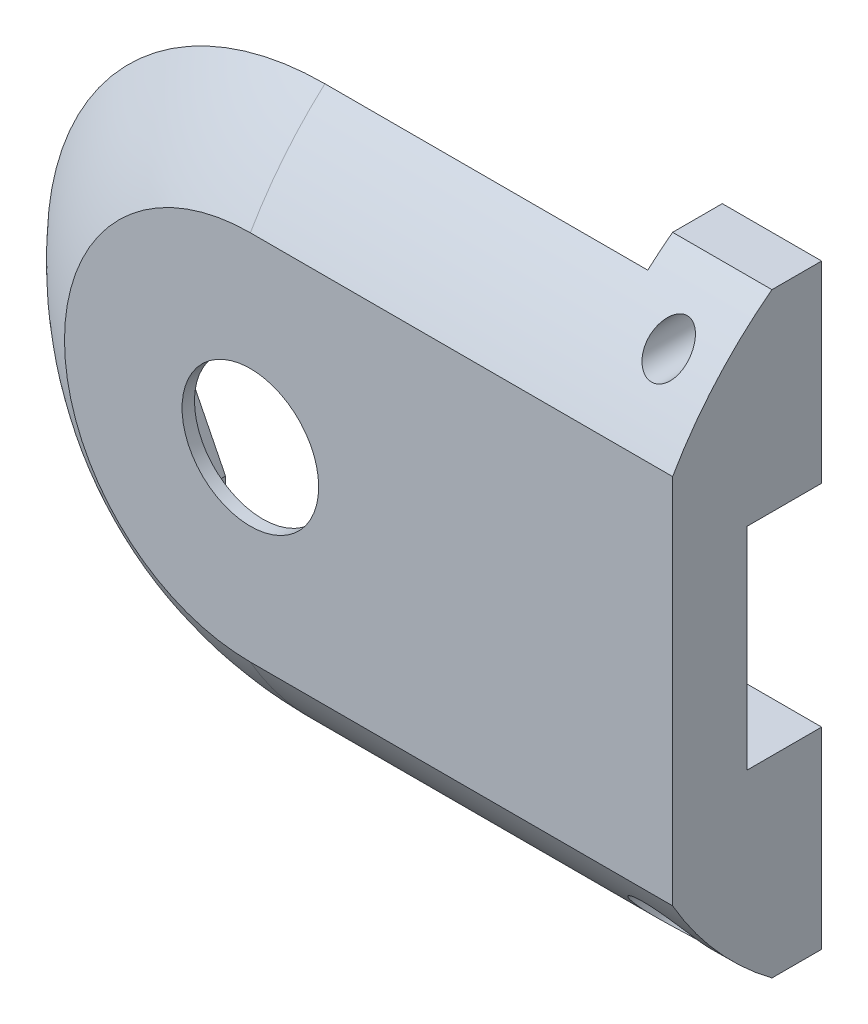
SolidWorks part; units mm, degrees
ref_plane "Front" through (0, 0, 0) normal (0, 0, 1) x (1, 0, 0)
ref_plane "Top" through (0, 0, 0) normal (0, 1, 0) x (1, 0, 0)
ref_plane "Right" through (0, 0, 0) normal (1, 0, 0) x (0, 0, -1)
sketch "Sketch1" plane through (0, 0, 0) normal (0, 0, 1) x (1, 0, 0)
  line L0 (13, 0) -> (17, 0) construction
  line L1 (17, 0) -> (17, 12)
  line L2 (17, 0) -> (17, -12)
  line L3 (0, 0) -> (38, 0) construction
  line L4 (17, 12) -> (5, 12)
  line L6 (17, -12) -> (5, -12)
  circle A0 centre (0, 0) radius 13
  circle A2 centre (0, 0) radius 2.75
extrude "Boss-Extrude1" add sketch "Sketch1" against normal blind 6
sketch "Sketch2" plane through (0, 0, 0) normal (0, 0, 1) x (1, 0, 0)
  line L0 (0, 13) -> (13, 13)
  line L1 (13, 0) -> (13, 4.25) construction
  line L2 (13, 0) -> (13, -4.25) construction
  line L3 (13, 13) -> (13, 0)
  line L4 (13, -4.25) -> (17, -4.25)
  line L5 (13, 0) -> (13, -13)
  line L6 (17, 12) -> (17, -12) construction
  line L7 (13, -13) -> (0, -13)
  line L8 (17, -4.25) -> (17, 4.25)
  line L9 (17, 4.25) -> (13, 4.25)
  circle A0 centre (0, 0) radius 13
extrude "Body Hole" cut sketch "Sketch2" against normal blind 3 from offset 3 offset against normal yes
sketch "Sketch8" plane through (28.2876, 0, 0) normal (0, 0, 1) x (1, 0, 0)
  line L26 (-28.2876, 0) -> (-35.2876, 0) construction
  line L27 (-28.2876, 0) -> (-18.7876, 0) construction
  line L28 (-28.2876, 0) -> (-28.2876, 5.5) construction
  line L29 (-28.2876, 0) -> (-28.2876, -5.5) construction
  line L30 (-35.2876, 0) -> (-35.2876, -1.5)
  line L31 (-35.2876, -1.5) -> (-33.7876, -1.5)
  line L32 (-33.7876, -1.5) -> (-32.2876, -1.5) construction
  line L33 (-32.2876, -1.5) -> (-32.2876, -4.5) construction
  line L34 (-33.7876, -1.5) -> (-32.2876, -4.5)
  line L35 (-32.2876, -4.5) -> (-32.2876, -5.5)
  line L36 (-32.2876, -5.5) -> (-28.2876, -5.5)
  line L37 (-28.2876, -5.5) -> (-24.0376, -5.5)
  line L38 (-24.0376, -5.5) -> (-24.0376, -4.5)
  line L39 (-24.0376, -4.5) -> (-18.7876, -4.5)
  line L40 (-18.7876, -4.5) -> (-18.7876, 0)
  line L41 (-35.2876, 0) -> (-35.2876, 1.5)
  line L42 (-35.2876, 1.5) -> (-33.7876, 1.5)
  line L43 (-33.7876, 1.5) -> (-32.2876, 1.5) construction
  line L44 (-32.2876, 1.5) -> (-32.2876, 4.5) construction
  line L45 (-33.7876, 1.5) -> (-32.2876, 4.5)
  line L46 (-32.2876, 4.5) -> (-32.2876, 5.5)
  line L47 (-32.2876, 5.5) -> (-28.2876, 5.5)
  line L48 (-28.2876, 5.5) -> (-24.0376, 5.5)
  line L49 (-24.0376, 5.5) -> (-24.0376, 4.5)
  line L50 (-24.0376, 4.5) -> (-18.7876, 4.5)
  line L51 (-18.7876, 4.5) -> (-18.7876, 0)
extrude "Pot Insert" cut sketch "Sketch8" along normal blind 2.5 from offset 3 offset against normal yes
sketch "Sketch3" plane through (0, 0, 0) normal (1, 0, 0) x (0, 0, -1)
  line L0 (0, 0) -> (13, 0) construction
  line L1 (0, 0) -> (-2, 0) construction
  line L2 (13, 15) -> (-2, 15)
  line L3 (-2, 15) -> (-2, 0)
  line L4 (-2, 0) -> (-2, -15)
  line L5 (-2, -15) -> (13, -15)
  circle A0 centre (13, 0) radius 15
extrude "Cut-Extrude2" cut sketch "Sketch3" along normal through all
sketch "Sketch6" plane through (0, 0, 0) normal (1, 0, 0) x (0, 0, -1)
  line L0 (0, 0) -> (13, 0) construction
  line L1 (0, 0) -> (-2, 0) construction
  line L2 (13, 15) -> (-2, 15)
  line L3 (-2, 15) -> (-2, 0)
  line L6 (-1, 5.3852) -> (-2, 5.3852)
  circle A0 centre (13, 0) radius 15
revolve "Cut-Revolve1" cut sketch "Sketch6" angle 180 about L0
sketch "Sketch7" plane through (0, 0, 0) normal (0, 0, 1) x (1, 0, 0)
  line L0 (17, 0) -> (13, 0) construction
  line L4 (15, 0) -> (15, 10) construction
  line L5 (15, 0) -> (15, -10) construction
  circle A0 centre (15, 10) radius 0.8
  circle A1 centre (15, -10) radius 0.8
extrude "Screw Holes" cut sketch "Sketch7" against normal through all
sketch "Sketch9" plane through (0, 0, 0) normal (0, 0, 1) x (1, 0, 0)
  circle A0 centre (15, -10) radius 1.25
extrude "Screw Heads" cut sketch "Sketch9" against normal blind 4
